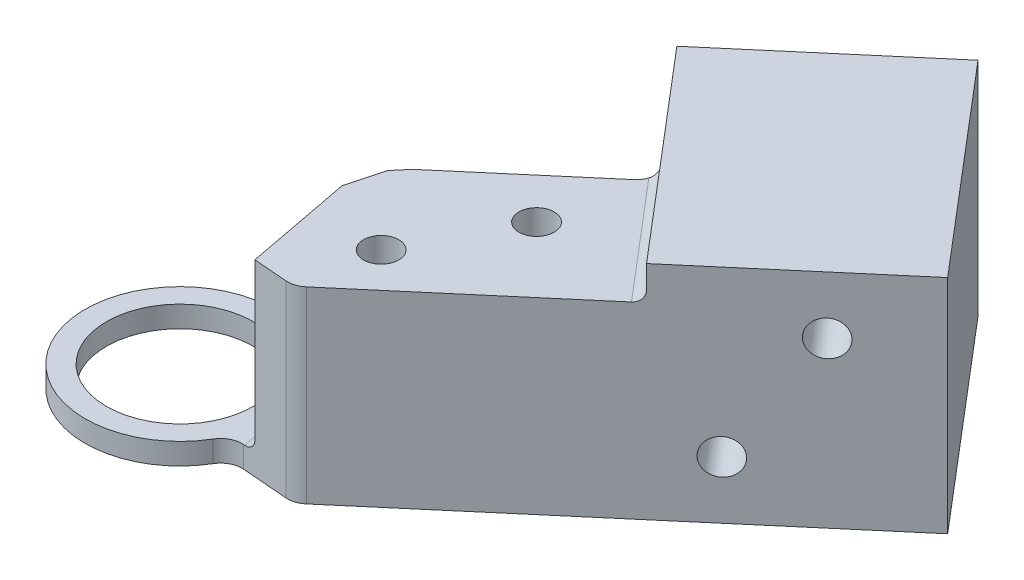
SolidWorks part; units mm, degrees
material "6061-T6 (SS)"
ref_plane "Front Plane" through (0, 0, 0) normal (0, 0, 1) x (1, 0, 0)
ref_plane "Top Plane" through (0, 0, 0) normal (0, 1, 0) x (1, 0, 0)
ref_plane "Right Plane" through (0, 0, 0) normal (1, 0, 0) x (0, 0, -1)
sketch "Sketch1" plane through (0, 0, 0) normal (0, 1, 0) x (1, 0, 0)
  circle A0 centre (0, 0) radius 12.5
  dimension "D2" = 25
extrude "Boss-Extrude1" add sketch "Sketch1" along normal blind 17.6
sketch "Sketch2" plane through (0, 17.6, 0) normal (0, 1, 0) x (1, 0, 0)
  circle A0 centre (0, 0) radius 6.875
  dimension "D1" = 13.75
extrude "Cut-Extrude1" cut sketch "Sketch2" against normal blind 50.8
sketch "Sketch3" plane through (0, 17.6, 0) normal (0, 1, 0) x (1, 0, 0)
  circle A0 centre (0, 0) radius 8.875
extrude "Cut-Extrude3" cut sketch "Sketch3" against normal offset from surface (15.6 mm away) 2 up to face at (0, 0, 6.875)
sketch "Sketch4" plane through (0, 17.6, 0) normal (0, 1, 0) x (1, 0, 0)
  line L0 (0, 0) -> (18.2932, 12.809)
  line L1 (0, 0) -> (-8.7404, 24.0142)
  line L2 (0, 0) -> (0, 22.9529) construction
  line L3 (0, 0) -> (-17.2058, 0) construction
  circle A0 centre (0, 0) radius 8.875 construction
  circle A1 centre (0, 0) radius 12.5 construction
  circle A2 centre (0, 0) radius 8.875
  circle A3 centre (0, 0) radius 12.5
  circle M3 centre (0, 0) radius 8.875
  circle M4 centre (0, 0) radius 12.5
  dimension "D1" = 75
  dimension "D2" = 55
extrude "Cut-Extrude4" cut sketch "Sketch4" against normal through all contours L1 L0 M3 M4
sketch "Sketch5" plane through (0, 17.6, 0) normal (0, 1, 0) x (1, 0, 0)
  line L0 (32.4721, 11.2168) -> (23.3996, 21.8794)
  line L1 (8.1004, -9.5202) -> (32.4721, 11.2168)
  line L4 (23.3996, 21.8794) -> (10.7177, 11.0888)
  line L5 (10.7177, 11.0888) -> (10.2394, 7.1697)
  arc A0 (-4.2753, 11.7462) -> (10.2394, 7.1697) centre (0, 0) ccw construction
  arc A1 (-4.8741, 11.5106) -> (10.2394, 7.1697) centre (0, 0) ccw
  dimension "D1" = 32
extrude "Boss-Extrude2" add sketch "Sketch5" against normal through all
fillet "Fillet1" radius 4 1 edges at (-3.0354, 9.8, -8.3398)
sketch "Sketch6" plane through (24.3717, 0, -20.737) normal (0.7616, 0, -0.648) x (-0.648, 0, -0.7616)
  line L1 (-12.5, 0) -> (12.5, 0)
  line L2 (-12.5, 0) -> (-12.5, 20.775)
  line L3 (-12.5, 20.775) -> (12.5, 20.775)
  line L4 (12.5, 0) -> (12.5, 20.775)
  point P4 (0, 0)
  dimension "D2" = 25
extrude "Boss-Extrude3" add sketch "Sketch6" along normal blind 20
hole_wizard "M4x0.7 Tapped Hole2" positions "Sketch7" profile "Sketch9" tap size "M4x0.7" standard "ANSI Metric"
sketch "Sketch7" plane through (-8.1004, 0, -9.5202) normal (-0.648, 0, -0.7616) x (-0.7616, 0, 0.648)
  line L0 (-44, 15.3875) -> (-37, 5.3875) construction
  line L2 (-32, 0) -> (-32, 20.775) construction
  line L3 (-52, 10.3875) -> (-28.7744, 10.3875) construction
  line L4 (-52, 0) -> (-52, 20.775) construction
  point P0 (-44, 15.3875)
  point P2 (-37, 5.3875)
  point P18 (-40.5, 10.3875)
  dimension "D1" = 7
  dimension "D2" = 10
  dimension "D3" = 5
sketch "Sketch9" plane through (25.4107, 15.3875, -38.0335) normal (0, 1, 0) x (-0.7616, 0, 0.648)
  line L0 (0, 0) -> (0, 7.9914)
  line L1 (0, 7.9914) -> (1.65, 7)
  line L2 (1.65, 7) -> (1.65, 0)
  line L5 (1.65, 0) -> (0, 0)
  line L10 (0, 7.9914) -> (-1.65, 7) construction
  line L11 (0, -6.35) -> (0, 107.95) construction
  dimension "Tap Drill Dia." = 3.3
  dimension "Tap Drill Depth" = 7
  dimension "Drill Angle" = 118
ref_plane "Plane1" through (0, 0, 0) normal (-0.648, 0, -0.7616) x (-0.7616, 0, 0.648)
mirror "Mirror1" about plane through (0, 0, 0) normal (-0.648, 0, -0.7616) of "M4x0.7 Tapped Hole2"
hole_wizard "M4x0.7 Tapped Hole1" positions "Sketch10" profile "Sketch11" tap size "M4x0.7" standard "ANSI Metric"
sketch "Sketch10" plane through (0, 17.6, 0) normal (0, 1, 0) x (1, 0, 0)
  line L5 (20.785, 12.6072) -> (13.1689, 6.1269)
  line L6 (13.1689, 6.1269) -> (15.761, 3.0804)
  line L7 (15.761, 3.0804) -> (20.785, 12.6072)
  line L9 (8.1004, -9.5202) -> (32.4721, 11.2168) construction
  line L11 (16.2713, 30.2571) -> (32.4721, 11.2168) construction
  point P0 (20.785, 12.6072)
  point P2 (15.761, 3.0804)
  dimension "D1" = 8.6325
  dimension "D2" = 10
  dimension "D3" = 4
  dimension "D4" = 8
sketch "Sketch11" plane through (20.785, 17.6, -12.6072) normal (1, 0, 0) x (0, 0, 1)
  line L0 (0, 0) -> (0, 7.9914)
  line L1 (0, 7.9914) -> (1.65, 7)
  line L2 (1.65, 7) -> (1.65, 0)
  line L5 (1.65, 0) -> (0, 0)
  line L10 (0, 7.9914) -> (-1.65, 7) construction
  line L11 (0, -6.35) -> (0, 107.95) construction
  dimension "Tap Drill Dia." = 3.3
  dimension "Tap Drill Depth" = 7
  dimension "Drill Angle" = 118
cosmetic thread "Hole Thread1" parameters "D1"=7, "D2"=4
cosmetic thread "Hole Thread2" parameters "D1"=7, "D2"=4
fillet "Fillet4" radius 1 1 edges at (27.9358, 17.6, -16.5481)
fillet "Fillet6" radius 1 2 edges at (-3.0354, 1, -8.3398) (7.27, 1, -5.0905)
fillet "Fillet7" radius 2 1 edges at (23.3996, 9.3, -21.8794)
sketch "Sketch13" plane through (0, 17.6, 0) normal (0, 1, 0) x (1, 0, 0)
  line L0 (8.0295, 3.7806) -> (11.3366, 16.1604)
  line L2 (8.0295, 3.7806) -> (7.0433, 5.3998)
  line L3 (7.0433, 5.3998) -> (5.7047, 6.7986)
  line L6 (10.7177, 11.0888) -> (10.2394, 7.1697) construction
  line L7 (11.3366, 16.1604) -> (5.7047, 6.7986)
  arc A0 (-5.4762, 6.984) -> (7.27, 5.0905) centre (0, 0) ccw construction
extrude "Cut-Extrude6" cut sketch "Sketch13" against normal up to surface (15.6 mm away) up to face at (0.802, 2, -5.5141)
fillet "Fillet8" radius 5 1 edges at (8.0295, 9.8, -3.7806)
sketch "Sketch14" plane through (0, 17.6, 0) normal (0, 1, 0) x (1, 0, 0)
  line L0 (8.6346, 6.046) -> (9.6428, 9.8199)
  line L1 (8.4434, 5.33) -> (8.6346, 6.046) construction
  line L2 (8.6346, 6.046) -> (10.2394, 7.1697) construction
  line L4 (10.7177, 11.0888) -> (10.2394, 7.1697) construction
  line L5 (10.2394, 7.1697) -> (8.6346, 6.046)
  line L6 (10.2394, 7.1697) -> (10.7177, 11.0888)
  line L7 (21.8764, 20.5833) -> (10.7177, 11.0888) construction
  line L8 (10.7177, 11.0888) -> (9.6428, 9.8199)
extrude "Boss-Extrude4" add sketch "Sketch14" against normal up to vertex (17.6 mm away)
sketch "Sketch15" plane through (0, 17.6, 0) normal (0, 1, 0) x (1, 0, 0)
  line L0 (8.1004, -9.5202) -> (31.7104, 10.5687) construction
  line L1 (8.1004, -9.5202) -> (11.1497, -6.9256)
  line L2 (8.1821, -3.4379) -> (11.1497, -6.9256)
  line L3 (-4.2753, 11.7462) -> (-2.1753, 8.6043)
  arc A0 (-4.2753, 11.7462) -> (8.1004, -9.5202) centre (0, 0) ccw
  arc A1 (-2.1753, 8.6043) -> (8.1821, -3.4379) centre (0, 0) ccw
  arc A2 (-5.4762, 6.984) -> (8.4906, 2.5838) centre (0, 0) ccw construction
  arc A3 (-5.4762, 6.984) -> (8.4906, 2.5838) centre (0, 0) ccw construction
  point P10 (7.7044, 2.1545)
  point P18 (7.7044, 2.1545)
  point P19 (0, 0)
  point P21 (7.999, 0.1284)
  point P22 (7.3754, -3.0989)
extrude "Cut-Extrude8" cut sketch "Sketch15" against normal through all
sketch "Sketch16" plane through (0, 17.6, 0) normal (0, 1, 0) x (1, 0, 0)
  line L0 (8.1821, -3.4379) -> (11.1497, -6.9256)
  line L1 (11.1497, -6.9256) -> (14.6375, -3.958)
  line L2 (11.1497, -6.9256) -> (31.7104, 10.5687) construction
  line L3 (8.1821, -3.4379) -> (14.6375, -3.958)
  line L4 (11.1497, -6.9256) -> (8.1821, -3.4379) construction
  dimension "D1" = 45
extrude "Cut-Extrude9" cut sketch "Sketch16" against normal through all
sketch "Sketch17" plane through (0, 17.6, 0) normal (0, 1, 0) x (1, 0, 0)
  line L1 (8.4434, 5.33) -> (9.6428, 9.8199) construction
  line L2 (8.7382, 6.4337) -> (10.6614, -3.6376)
  line L3 (14.6375, -3.958) -> (8.1821, -3.4379) construction
  line L4 (10.6614, -3.6376) -> (8.1821, -3.4379)
  line L5 (8.1821, -3.4379) -> (7.9514, 5.9104)
  line L6 (7.9514, 5.9104) -> (8.7382, 6.4337)
extrude "Cut-Extrude10" cut sketch "Sketch17" against normal up to surface (15.6 mm away) up to face at (5.4339, 2, -3.1833)
fillet "Fillet10" radius 1 1 edges at (8.6346, 1, -6.046)
fillet "Fillet12" radius 1 1 edges at (9.6998, 2, -1.398)
fillet "Fillet13" radius 2 2 edges at (8.1821, 1, 3.4379) (14.6375, 8.8, 3.958)
equation "\"1.1c\"=0.0104601"
